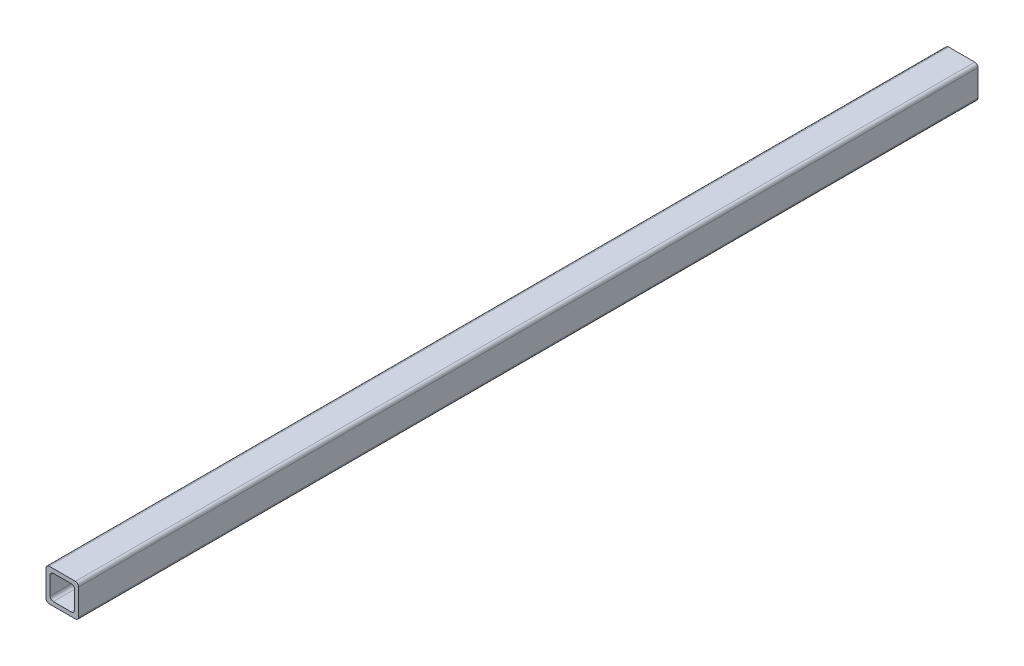
SolidWorks part; units mm, degrees
ref_plane "Alzado" through (0, 0, 0) normal (0, 0, 1) x (1, 0, 0)
ref_plane "Planta" through (0, 0, 0) normal (0, 1, 0) x (1, 0, 0)
ref_plane "Vista lateral" through (0, 0, 0) normal (1, 0, 0) x (0, 0, -1)
sketch "Croquis1" plane through (0, 0, 0) normal (0, 0, 1) x (1, 0, 0)
  line L1 (-7.025, -9.525) -> (7.025, -9.525)
  line L2 (-9.525, -7.025) -> (-9.525, 7.025)
  line L3 (-7.025, 9.525) -> (7.025, 9.525)
  line L4 (9.525, -7.025) -> (9.525, 7.025)
  line L5 (-9.525, -9.525) -> (9.525, 9.525) construction
  line L6 (-9.525, 9.525) -> (9.525, -9.525) construction
  line L7 (-10.2, -12.7) -> (10.2, -12.7)
  line L8 (-12.7, -10.2) -> (-12.7, 10.2)
  line L9 (-10.2, 12.7) -> (10.2, 12.7)
  line L10 (12.7, -10.2) -> (12.7, 10.2)
  line L11 (-12.7, -12.7) -> (12.7, 12.7) construction
  line L12 (-12.7, 12.7) -> (12.7, -12.7) construction
  arc A0 (-7.025, -9.525) -> (-9.525, -7.025) centre (-7.025, -7.025) cw
  arc A1 (7.025, -9.525) -> (9.525, -7.025) centre (7.025, -7.025) ccw
  arc A2 (9.525, 7.025) -> (7.025, 9.525) centre (7.025, 7.025) ccw
  arc A3 (12.7, -10.2) -> (10.2, -12.7) centre (10.2, -10.2) cw
  arc A4 (-10.2, -12.7) -> (-12.7, -10.2) centre (-10.2, -10.2) cw
  arc A5 (12.7, 10.2) -> (10.2, 12.7) centre (10.2, 10.2) ccw
  arc A6 (-9.525, 7.025) -> (-7.025, 9.525) centre (-7.025, 7.025) cw
  arc A7 (-10.2, 12.7) -> (-12.7, 10.2) centre (-10.2, 10.2) ccw
  point P0 (0, 0)
  point P6 (0, 0)
  dimension "D3" = 2.5
  dimension "D1" = 25.4
  dimension "D2" = 3.175
extrude "Saliente-Extruir1" add sketch "Croquis1" along normal blind 700
